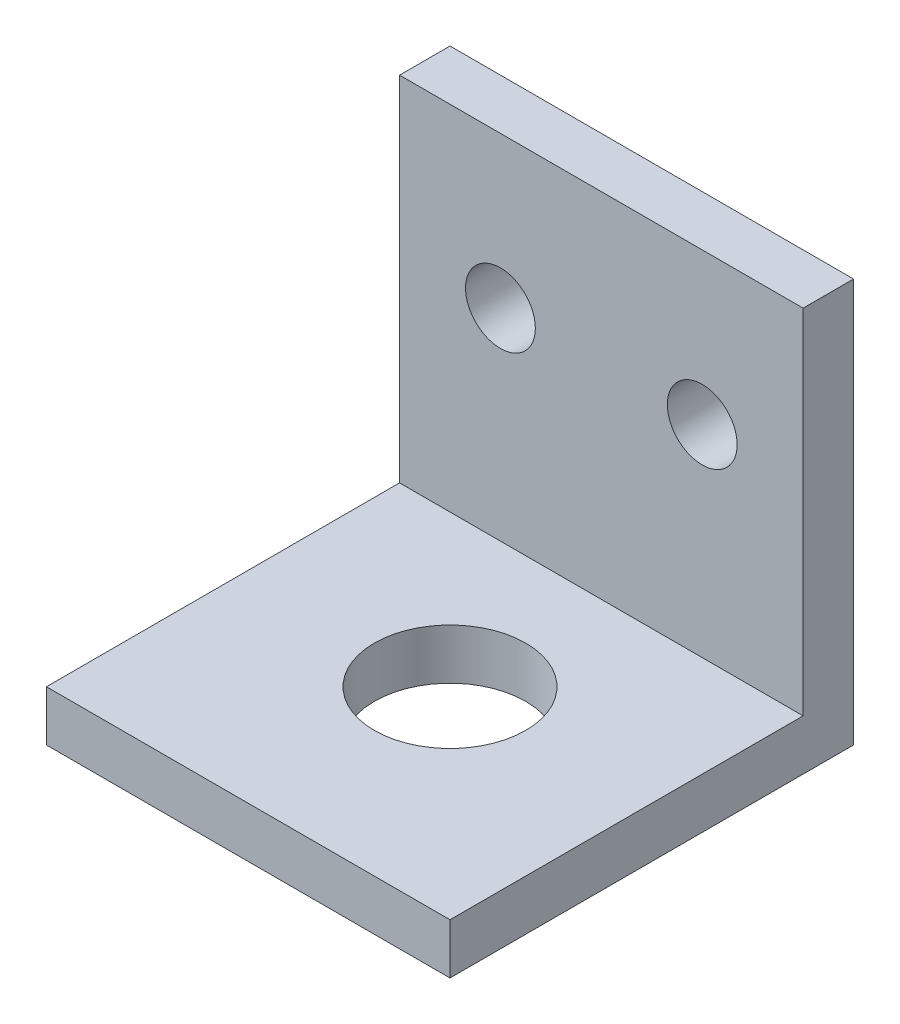
SolidWorks part; units mm, degrees
ref_plane "Front Plane" through (0, 0, 0) normal (0, 0, 1) x (1, 0, 0)
ref_plane "Top Plane" through (0, 0, 0) normal (0, 1, 0) x (1, 0, 0)
ref_plane "Right Plane" through (0, 0, 0) normal (1, 0, 0) x (0, 0, -1)
sketch "Sketch1" plane through (0, 0, 0) normal (0, 1, 0) x (1, 0, 0)
  line L1 (-12.7, -12.7) -> (12.7, -12.7)
  line L2 (-12.7, -12.7) -> (-12.7, 12.7)
  line L3 (-12.7, 12.7) -> (12.7, 12.7)
  line L4 (12.7, -12.7) -> (12.7, 12.7)
  line L5 (-12.7, -12.7) -> (12.7, 12.7) construction
  line L6 (-12.7, 12.7) -> (12.7, -12.7) construction
  point P0 (0, 0)
  dimension "D1" = 25.4
  dimension "D2" = 25.4
extrude "Boss-Extrude1" add sketch "Sketch1" along normal blind 3.175 contours L3 L4 L1 L2
sketch "Sketch2" plane through (0, 0, 0) normal (0, -1, 0) x (1, 0, 0)
  line L0 (-12.7, 12.7) -> (-12.7, -12.7) construction
  line L1 (12.7, -12.7) -> (-12.7, -12.7)
  line L2 (12.7, -12.7) -> (12.7, -9.525)
  line L3 (12.7, -9.525) -> (-12.7, -9.525)
  line L4 (-12.7, -12.7) -> (-12.7, -9.525)
  dimension "D1" = 3.175
extrude "Boss-Extrude2" add sketch "Sketch2" against normal blind 25.4
sketch "Sketch3" plane through (0, 3.175, 0) normal (0, 1, 0) x (1, 0, 0)
  circle A0 centre (0, 0) radius 4.7625
  dimension "D1" = 9.525
extrude "Cut-Extrude1" cut sketch "Sketch3" against normal through all contours A0
sketch "Sketch4" plane through (0, 0, -9.525) normal (0, 0, 1) x (1, 0, 0)
  line L0 (-12.7, 25.4) -> (-12.7, 3.175) construction
  line L1 (0, 25.4) -> (0, 3.175) construction
  line L2 (12.7, 25.4) -> (-12.7, 25.4) construction
  line L3 (12.7, 3.175) -> (-12.7, 3.175) construction
  circle A0 centre (-6.35, 15.875) radius 2.1971
  circle A1 centre (6.35, 15.875) radius 2.1971
  dimension "D1" = 4.3942
  dimension "D2" = 6.35
  dimension "D3" = 9.525
extrude "Cut-Extrude2" cut sketch "Sketch4" against normal through all
sketch "Sketch5" [suppressed] plane through (0, 3.175, 0) normal (0, 1, 0) x (1, 0, 0)
  line L0 (-12.7, 12.7) -> (12.7, 12.7) construction
  circle A0 centre (0, -3.175) radius 4.7625
  dimension "D2" = 9.525
  dimension "D1" = 15.875
extrude "Cut-Extrude3" [suppressed] cut sketch "Sketch5" against normal through all
equation "\"D1@Sketch2\"=\"D1@Boss-Extrude1\""
